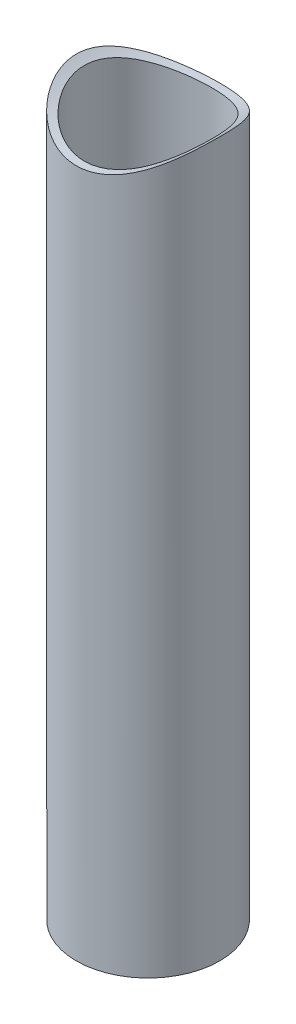
SolidWorks part; units mm, degrees
ref_plane "Front Plane" through (0, 0, 0) normal (0, 0, 1) x (1, 0, 0)
ref_plane "Top Plane" through (0, 0, 0) normal (0, 1, 0) x (1, 0, 0)
ref_plane "Right Plane" through (0, 0, 0) normal (1, 0, 0) x (0, 0, -1)
sketch "Sketch1" plane through (0, 0, 0) normal (0, 1, 0) x (1, 0, 0)
  circle A0 centre (0, 0) radius 7.9375
  circle A1 centre (0, 0) radius 7.0485
  dimension "D1" = 15.875
  dimension "D2" = 0.889
extrude "Boss-Extrude1" add sketch "Sketch1" along normal blind 88.9
sketch "Sketch2" plane through (0, 0, 0) normal (0, 0, 1) x (1, 0, 0)
  line L0 (7.0485, 88.9) -> (-7.0485, 88.9) construction
  circle A0 centre (0, 88.9) radius 12.7
  dimension "D1" = 25.4
extrude "Cut-Extrude1" cut sketch "Sketch2" against normal through all and the other way through all contours A0
